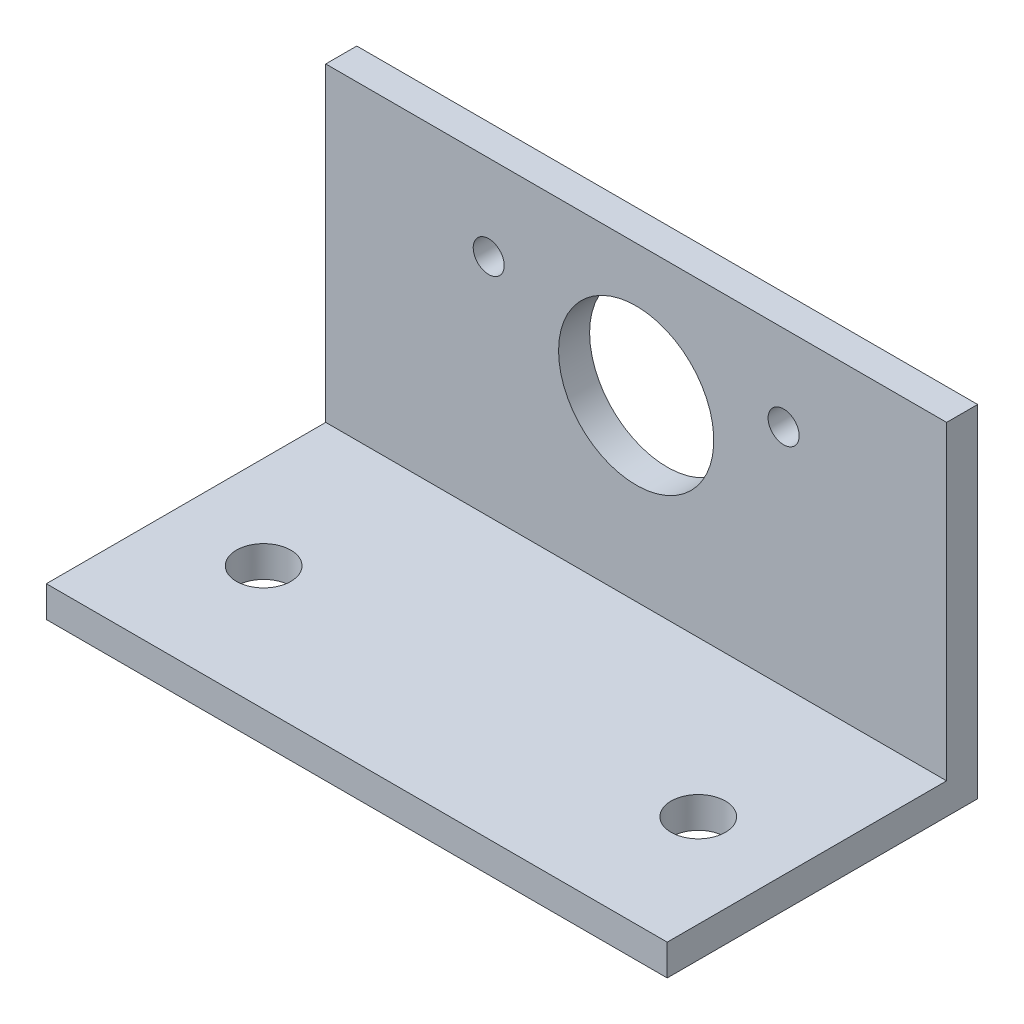
SolidWorks part; units mm, degrees
ref_plane "Front Plane" through (0, 0, 0) normal (0, 0, 1) x (1, 0, 0)
ref_plane "Top Plane" through (0, 0, 0) normal (0, 1, 0) x (1, 0, 0)
ref_plane "Right Plane" through (0, 0, 0) normal (1, 0, 0) x (0, 0, -1)
sketch "Sketch1" plane through (0, 0, 0) normal (0, 1, 0) x (1, 0, 0)
  line L1 (-20, 10) -> (20, 10)
  line L2 (-20, 10) -> (-20, -10)
  line L3 (-20, -10) -> (20, -10)
  line L4 (20, 10) -> (20, -10)
  line L5 (-20, 10) -> (20, -10) construction
  line L6 (-20, -10) -> (20, 10) construction
  point P0 (0, 0)
  dimension "D1" = 40
  dimension "D2" = 20
extrude "Boss-Extrude1" add sketch "Sketch1" along normal blind 2
sketch "Sketch2" plane through (0, 2, 0) normal (0, 1, 0) x (1, 0, 0)
  line L0 (20, -10) -> (20, 10) construction
  line L1 (-20, 10) -> (20, 10)
  line L2 (-20, 10) -> (-20, 8)
  line L3 (-20, 8) -> (20, 8)
  line L4 (20, 10) -> (20, 8)
  dimension "D1" = 2
extrude "Boss-Extrude2" add sketch "Sketch2" along normal blind 20
sketch "Sketch3" plane through (0, 0, 0) normal (0, -1, 0) x (1, 0, 0)
  line L0 (20, -10) -> (-20, -10) construction
  line L1 (-20, -10) -> (-20, 10) construction
  line L2 (20, 10) -> (20, -10) construction
  circle A0 centre (-14, 2) radius 1.75
  circle A1 centre (14, 2) radius 1.75
  dimension "D5" = 3.5
  dimension "D6" = 3.5
  dimension "D1" = 12
  dimension "D2" = 6
  dimension "D3" = 6
  dimension "D4" = 12
extrude "Cut-Extrude1" cut sketch "Sketch3" against normal through all
sketch "Sketch4" plane through (0, 0, -10) normal (0, 0, -1) x (-1, 0, 0)
  line L1 (-20, 0) -> (20, 0) construction
  circle A0 centre (0, 13.5) radius 5
  circle A1 centre (-9.5, 16.5) radius 1
  circle A2 centre (9.5, 16.5) radius 1
  dimension "D2" = 10
  dimension "D1" = 13.5
  dimension "D3" = 9.5
  dimension "D4" = 16.5
  dimension "D5" = 16.5
  dimension "D6" = 9.5
  dimension "D7" = 3
extrude "Cut-Extrude2" cut sketch "Sketch4" against normal through all
